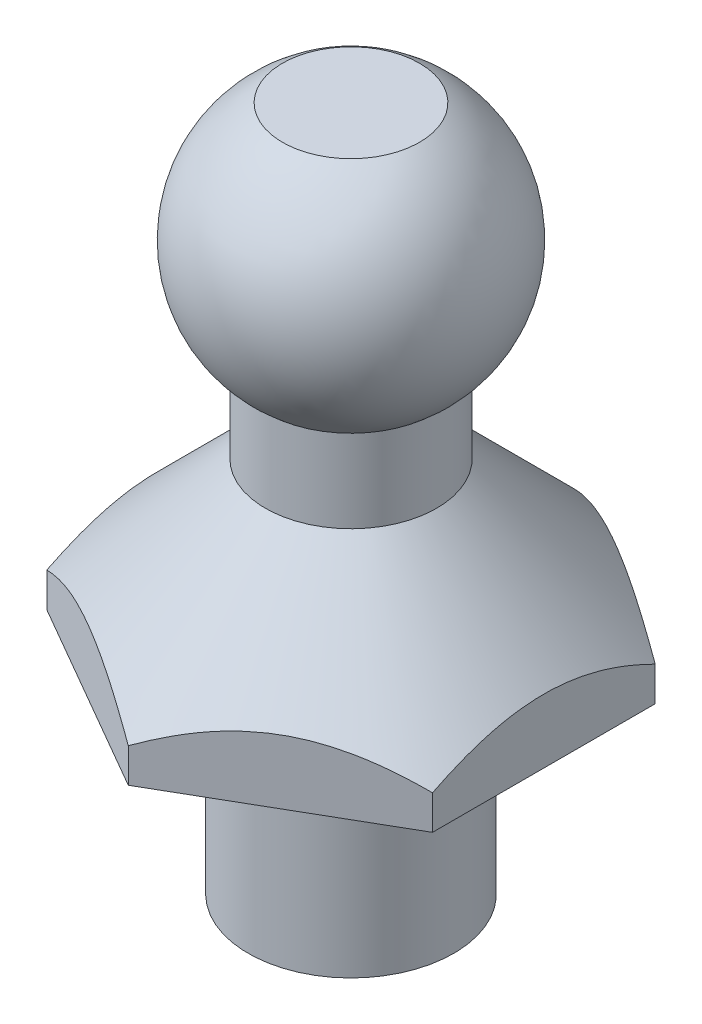
SolidWorks part; units mm, degrees
material "Stainless Steel (ferritic)"
ref_plane "Front Plane" through (0, 0, 0) normal (0, 0, 1) x (1, 0, 0)
ref_plane "Top Plane" through (0, 0, 0) normal (0, 1, 0) x (1, 0, 0)
ref_plane "Right Plane" through (0, 0, 0) normal (1, 0, 0) x (0, 0, -1)
sketch "Sketch1" plane through (0, 0, 0) normal (0, 0, 1) x (1, 0, 0)
  line L0 (0, 5.5) -> (0, 10)
  line L1 (0, 5.5) -> (1.25, 5.5)
  line L2 (1.25, 5.5) -> (1.25, 6.7067)
  line L3 (0, 10.2679) -> (-1.4696, 10.2679) construction
  line L4 (0, 10) -> (1, 10)
  line L5 (1.25, 5.5) -> (3.25, 3.5)
  line L6 (3.25, 3.5) -> (3.25, 3)
  line L7 (3.25, 3) -> (1.5, 3)
  line L8 (1.5, 3) -> (1.5, 0)
  line L9 (1.5, 0) -> (0, 0)
  line L10 (0, 0) -> (0, 5.5)
  arc A0 (1, 10) -> (1.25, 6.7067) centre (0, 8.2679) cw
  arc A1 (1, 10) -> (0, 10.2679) centre (0, 8.2679) ccw construction
  dimension "D2" = 2
  dimension "D1" = 1
  dimension "D3" = 1.25
  dimension "D4" = 4.5
  dimension "D5" = 3.25
  dimension "D6" = 135
  dimension "D7" = 3
  dimension "D8" = 1.5
  dimension "D9" = 0.5
revolve "Revolve3" add sketch "Sketch1" angle 360 about L0
sketch "Sketch3" plane through (0, 3, 0) normal (0, -1, 0) x (1, 0, 0)
  line L1 (0, 3.25) -> (-2.8146, 1.625)
  line L2 (-2.8146, 1.625) -> (-2.8146, -1.625)
  line L3 (-2.8146, -1.625) -> (0, -3.25)
  line L4 (0, -3.25) -> (2.8146, -1.625)
  line L5 (2.8146, -1.625) -> (2.8146, 1.625)
  line L6 (2.8146, 1.625) -> (0, 3.25)
  circle A0 centre (0, 0) radius 2.8146 construction
  circle A2 centre (0, 0) radius 3.25 construction
extrude "Cut-Extrude1" cut sketch "Sketch3" against normal through all flip side to cut
equation "\"e\"=4.82414"
